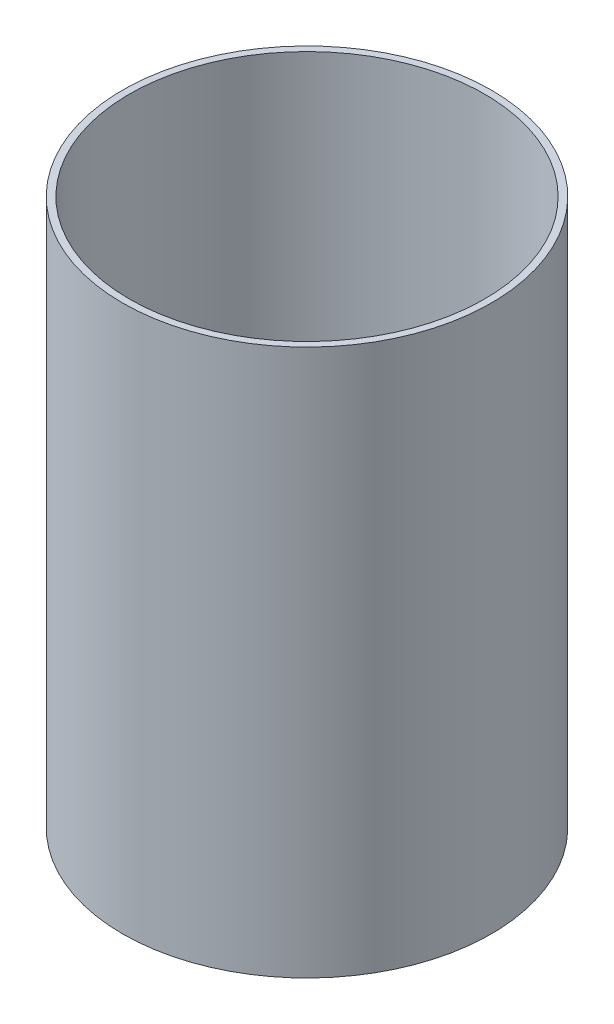
SolidWorks part; units mm, degrees
ref_plane "Front" through (0, 0, 0) normal (0, 0, 1) x (1, 0, 0)
ref_plane "Top" through (0, 0, 0) normal (0, 1, 0) x (1, 0, 0)
ref_plane "Right" through (0, 0, 0) normal (1, 0, 0) x (0, 0, -1)
sketch "Sketch1" plane through (0, 0, 0) normal (0, 1, 0) x (1, 0, 0)
  circle A0 centre (0, 0) radius 66.04
  circle A1 centre (0, 0) radius 68.58
  dimension "D1" = 132.08
  dimension "D2" = 137.16
extrude "Boss-Extrude1" add sketch "Sketch1" along normal blind 203.2
